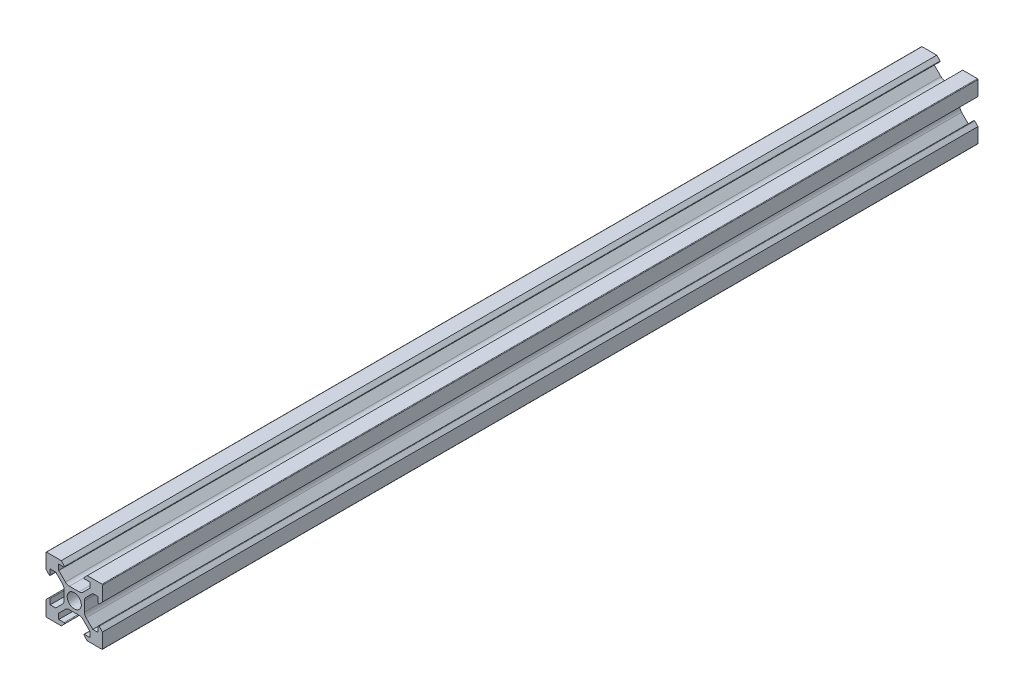
SolidWorks part; units mm, degrees
material "Liga 1350"
ref_plane "Plano frontal" through (0, 0, 0) normal (0, 0, 1) x (1, 0, 0)
ref_plane "Plano superior" through (0, 0, 0) normal (0, 1, 0) x (1, 0, 0)
ref_plane "Plano direito" through (0, 0, 0) normal (1, 0, 0) x (0, 0, -1)
sketch "Esboço1" plane through (0, 0, 0) normal (0, 0, 1) x (1, 0, 0)
  line L0 (0, 13.8681) -> (0, -15.879) construction
  line L1 (-4.6, -10) -> (-9.8, -10)
  line L2 (-3.4414, -8.8414) -> (-4.6, -10)
  line L3 (-4.1858, -3.1251) -> (-6.5607, -5.5)
  line L4 (-10, 9.8) -> (-10, 4.6)
  line L5 (-5.5, -8.5) -> (-3.5828, -8.5)
  line L6 (-5.5, -8.5) -> (-5.5, -6.5607)
  line L7 (-8.5, -5.5) -> (-8.5, -3.5828)
  line L8 (-21.5514, 0) -> (2.5, 0) construction
  line L9 (-3.1251, 4.1858) -> (-5.5, 6.5607)
  line L10 (-8.8414, -3.4414) -> (-10, -4.6)
  line L11 (-8.5, 5.5) -> (-6.5607, 5.5)
  line L12 (-8.8414, 3.4414) -> (-10, 4.6)
  line L13 (-8.5, -5.5) -> (-6.5607, -5.5)
  line L14 (-8.5, 5.5) -> (-8.5, 3.5828)
  line L15 (-3.1251, -4.1858) -> (-5.5, -6.5607)
  line L16 (-21.5514, 0) -> (20.6623, 0) construction
  line L17 (-8.5, 10) -> (-8.5, -10) construction
  line L18 (-10, -9.8) -> (-10, -4.6)
  line L19 (-21.5514, 5.5) -> (20.6623, 5.5) construction
  line L21 (-10, 10) -> (-10, -10) construction
  line L22 (3.6, 1.7109) -> (3.6, 0) construction
  line L23 (21.5514, 0) -> (-2.5, 0) construction
  line L24 (4.6, 10) -> (9.8, 10)
  line L25 (-5.5, 8.5) -> (-5.5, 6.5607)
  line L26 (3.4414, 8.8414) -> (4.6, 10)
  line L27 (-5.5, 8.5) -> (-3.5828, 8.5)
  line L28 (4.1858, 3.1251) -> (6.5607, 5.5)
  line L29 (5.5, 8.5) -> (3.5828, 8.5)
  line L30 (5.5, 8.5) -> (5.5, 6.5607)
  line L31 (-3.6, 1.7109) -> (-3.6, -1.7109)
  line L33 (10, -9.8) -> (10, -4.6)
  line L34 (-4.1858, 3.1251) -> (-6.5607, 5.5)
  line L35 (-3.4414, 8.8414) -> (-4.6, 10)
  line L36 (-4.6, 10) -> (-9.8, 10)
  line L37 (3.1251, -4.1858) -> (5.5, -6.5607)
  line L38 (8.5, 5.5) -> (8.5, 3.5828)
  line L39 (8.5, -5.5) -> (6.5607, -5.5)
  line L40 (8.8414, 3.4414) -> (10, 4.6)
  line L41 (8.5, 5.5) -> (6.5607, 5.5)
  line L42 (8.8414, -3.4414) -> (10, -4.6)
  line L43 (3.1251, 4.1858) -> (5.5, 6.5607)
  line L44 (8.5, -5.5) -> (8.5, -3.5828)
  line L45 (5.5, -8.5) -> (5.5, -6.5607)
  line L46 (5.5, -8.5) -> (3.5828, -8.5)
  line L47 (10, 9.8) -> (10, 4.6)
  line L48 (4.1858, -3.1251) -> (6.5607, -5.5)
  line L49 (3.4414, -8.8414) -> (4.6, -10)
  line L50 (4.6, -10) -> (9.8, -10)
  line L51 (-1.7109, 3.6) -> (1.7109, 3.6)
  line L52 (3.6, 1.7109) -> (3.6, -1.7109)
  line L53 (1.7109, -3.6) -> (-1.7109, -3.6)
  circle A0 centre (0, 0) radius 2.5
  arc A1 (-3.6, 1.7109) -> (-4.1858, 3.1251) centre (-5.6, 1.7109) ccw
  arc A2 (-8.5, 3.5828) -> (-8.8414, 3.4414) centre (-8.7, 3.5828) cw
  arc A3 (-9.8, 10) -> (-10, 9.8) centre (-9.8, 9.8) ccw
  arc A4 (-1.7109, 3.6) -> (-3.1251, 4.1858) centre (-1.7109, 5.6) cw
  arc A5 (-3.5828, 8.5) -> (-3.4414, 8.8414) centre (-3.5828, 8.7) ccw
  arc A6 (-3.5828, -8.5) -> (-3.4414, -8.8414) centre (-3.5828, -8.7) cw
  arc A7 (-1.7109, -3.6) -> (-3.1251, -4.1858) centre (-1.7109, -5.6) ccw
  arc A8 (-9.8, -10) -> (-10, -9.8) centre (-9.8, -9.8) cw
  arc A9 (-8.5, -3.5828) -> (-8.8414, -3.4414) centre (-8.7, -3.5828) ccw
  arc A10 (-3.6, -1.7109) -> (-4.1858, -3.1251) centre (-5.6, -1.7109) cw
  arc A11 (3.6, -1.7109) -> (4.1858, -3.1251) centre (5.6, -1.7109) ccw
  arc A12 (8.5, -3.5828) -> (8.8414, -3.4414) centre (8.7, -3.5828) cw
  arc A13 (9.8, -10) -> (10, -9.8) centre (9.8, -9.8) ccw
  arc A14 (1.7109, -3.6) -> (3.1251, -4.1858) centre (1.7109, -5.6) cw
  arc A15 (3.5828, -8.5) -> (3.4414, -8.8414) centre (3.5828, -8.7) ccw
  arc A16 (3.5828, 8.5) -> (3.4414, 8.8414) centre (3.5828, 8.7) cw
  arc A17 (1.7109, 3.6) -> (3.1251, 4.1858) centre (1.7109, 5.6) ccw
  arc A18 (9.8, 10) -> (10, 9.8) centre (9.8, 9.8) cw
  arc A19 (8.5, 3.5828) -> (8.8414, 3.4414) centre (8.7, 3.5828) ccw
  arc A20 (3.6, 1.7109) -> (4.1858, 3.1251) centre (5.6, 1.7109) cw
  point P0 (0, 0)
  point P45 (-3.6, 2.5393)
extrude "Ressalto-extrusão1" add sketch "Esboço1" along normal blind 310
